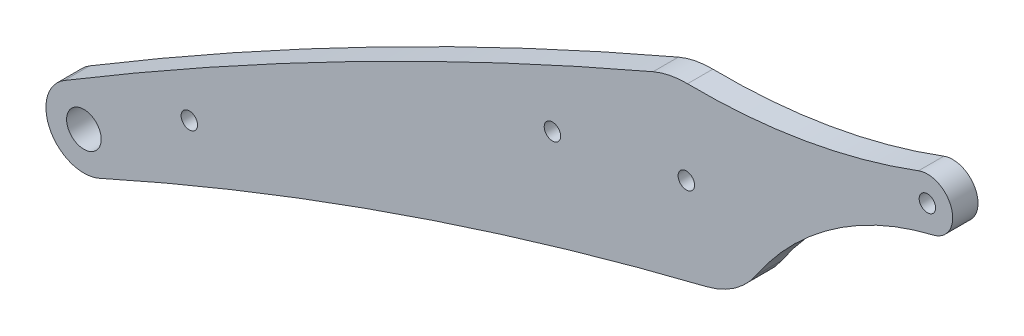
SolidWorks part; units mm, degrees
ref_plane "Front Plane" through (0, 0, 0) normal (0, 0, 1) x (1, 0, 0)
ref_plane "Top Plane" through (0, 0, 0) normal (0, 1, 0) x (1, 0, 0)
ref_plane "Right Plane" through (0, 0, 0) normal (1, 0, 0) x (0, 0, -1)
sketch "Sketch1" plane through (0, 0, 0) normal (0, 0, 1) x (1, 0, 0)
  line L1 (-44.9038, 204.7832) -> (-244.9038, 119.9638) construction
  arc A0 (-249.5477, 127.6731) -> (-241.2152, 111.7544) centre (-244.9038, 119.9638) ccw
  circle A1 centre (-102.0625, 180.8918) radius 1.95
  circle A2 centre (-102.0625, 180.8918) radius 20 construction
  arc A3 (-43.51, 198.9474) -> (-47.0081, 210.4021) centre (-44.9038, 204.7832) ccw
  arc A4 (-249.5477, 127.6731) -> (-109.9547, 199.2688) centre (343.8459, -857.4076) cw
  arc A5 (-97.253, 161.4787) -> (-241.2152, 111.7544) centre (107.152, -663.578) ccw
  arc A6 (-85.4373, 169.7741) -> (-43.51, 198.9474) centre (-27.2491, 130.8622) cw
  arc A7 (-101.7747, 200.8897) -> (-47.0081, 210.4021) centre (-99.616, 350.8742) ccw
  arc A8 (-109.9547, 199.2688) -> (-101.7747, 200.8897) centre (-102.0625, 180.8918) cw
  arc A9 (-97.253, 161.4787) -> (-85.4373, 169.7741) centre (-102.0625, 180.8918) ccw
  arc A10 (-244.9038, 119.9638) -> (-44.9038, 204.7832) centre (160.6116, -558.0165) cw construction
  circle A11 centre (-44.9038, 204.7832) radius 1.95
  circle A12 centre (-244.9038, 119.9638) radius 4.1
  circle A13 centre (-219.9038, 134.3042) radius 1.95
  circle A14 centre (-133.8125, 175.069) radius 1.95
  point P0 (-102.0625, 180.8918)
  point P22 (-133.8125, 175.069)
  point P23 (-219.9038, 134.3042)
  dimension "D1" = 18
  dimension "D2" = 12
  dimension "D3" = 3.9
  dimension "D4" = 40
  dimension "D5" = 850
  dimension "D6" = 1150
  dimension "D7" = 150
  dimension "D8" = 70
  dimension "D9" = 790
  dimension "D10" = 25
  dimension "D12" = 8.2
  dimension "D13" = 3.9
  dimension "D14" = 3.9
  dimension "D15" = 3.9
  dimension "D11" = 31.75
  dimension "D16" = 200
extrude "Boss-Extrude1" add sketch "Sketch1" along normal blind 6
